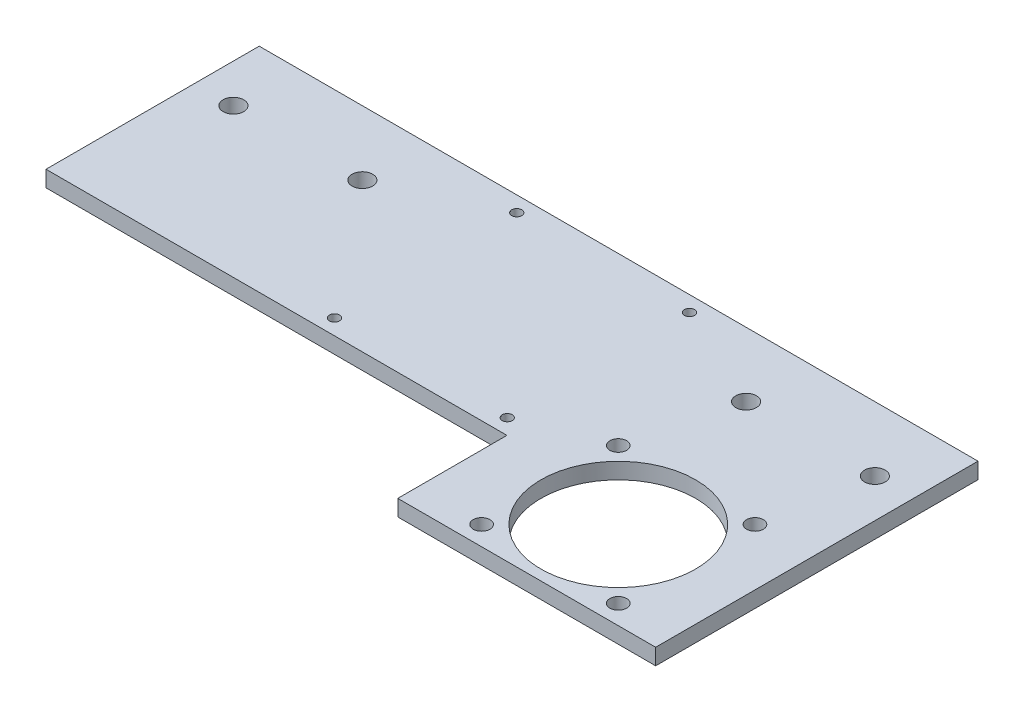
SolidWorks part; units mm, degrees
ref_plane "Front Plane" through (0, 0, 0) normal (0, 0, 1) x (1, 0, 0)
ref_plane "Top Plane" through (0, 0, 0) normal (0, 1, 0) x (1, 0, 0)
ref_plane "Right Plane" through (0, 0, 0) normal (1, 0, 0) x (0, 0, -1)
sketch "Sketch1" plane through (0, 0, 0) normal (0, 1, 0) x (1, 0, 0)
  line L1 (20, -21) -> (-20, -21)
  line L2 (20, -21) -> (20, 21)
  line L3 (20, 21) -> (-20, 21)
  line L4 (-20, -21) -> (-20, 21)
  line L5 (20, -21) -> (-20, 21) construction
  line L6 (20, 21) -> (-20, -21) construction
  point P0 (0, 0)
  dimension "D1" = 40
  dimension "D2" = 42
extrude "Boss-Extrude1" add sketch "Sketch1" along normal blind 3.175
sketch "Sketch2" plane through (0, 3.175, 0) normal (0, 1, 0) x (1, 0, 0)
  line L0 (20, -21) -> (20, 21) construction
  line L1 (-20, -21) -> (20, -21) construction
  line L2 (0, -21) -> (0, 21) construction
  line L3 (20, 21) -> (-20, 21) construction
  line L4 (20, 0) -> (-20, 0) construction
  line L5 (-20, 21) -> (-20, -21) construction
  line L6 (20, -21) -> (-20, -21) construction
  circle A0 centre (17.016, -17.952) radius 1
  circle A1 centre (-17.016, -17.952) radius 1
  circle A2 centre (17.016, 17.952) radius 1
  circle A3 centre (-17.016, 17.952) radius 1
  dimension "D1" = 2
  dimension "D2" = 17.016
  dimension "D3" = 3.048
extrude "Cut-Extrude1" cut sketch "Sketch2" against normal through all
sketch "Sketch3" plane through (0, 3.175, 0) normal (0, 1, 0) x (1, 0, 0)
  line L0 (20, 21) -> (-20, 21) construction
  line L1 (20, -42.5) -> (70.8, -42.5)
  line L2 (20, -42.5) -> (20, 21)
  line L3 (20, 21) -> (70.8, 21)
  line L4 (70.8, -42.5) -> (70.8, 21)
  line L5 (-20, 21) -> (-70.8, 21)
  line L6 (-20, 21) -> (-20, -42.5)
  line L7 (-20, -42.5) -> (-70.8, -42.5)
  line L8 (-70.8, 21) -> (-70.8, -42.5)
  line L10 (-20, -42.5) -> (-20, -67.9)
  dimension "D1" = 50.8
  dimension "D2" = 50.8
  dimension "D4" = 63.5
extrude "Boss-Extrude2" add sketch "Sketch3" against normal blind 3.175
sketch "Sketch4" plane through (0, 3.175, 0) normal (0, 1, 0) x (1, 0, 0)
  line L0 (70.8, 21) -> (-70.8, 21) construction
  line L1 (70.8, -42.5) -> (70.8, 21) construction
  line L2 (-70.8, 21) -> (-70.8, -42.5) construction
  circle A0 centre (63.18, 8.3) radius 2.032
  circle A1 centre (37.8145, 8.3) radius 2.032
  circle A2 centre (-37.78, 8.3) radius 2.032
  circle A3 centre (-63.18, 8.3) radius 2.032
  dimension "D1" = 4.064
  dimension "D6" = 4.064
  dimension "D7" = 4.064
  dimension "D8" = 4.064
  dimension "D2" = 12.7
  dimension "D3" = 7.62
  dimension "D4" = 25.3655
  dimension "D5" = 25.4
  dimension "D9" = 7.62
extrude "Cut-Extrude2" cut sketch "Sketch4" against normal through all
sketch "Sketch7" plane through (0, 0, 0) normal (0, -1, 0) x (1, 0, 0)
  line L0 (0, 21) -> (0, -21) construction
  line L1 (-20, 21) -> (20, 21) construction
  line L2 (70.8, -21) -> (-70.8, -21) construction
  line L3 (-70.8, 0) -> (70.8, 0) construction
  line L4 (-70.8, -21) -> (-70.8, 42.5) construction
  line L5 (70.8, 42.5) -> (70.8, -21) construction
sketch "Sketch8" plane through (0, 0, 0) normal (0, -1, 0) x (-1, 0, 0)
  line L0 (-20, -42.5) -> (-70.8, -42.5) construction
  line L1 (-20, -42.5) -> (-20, -21) construction
  line L2 (-70.8, -42.5) -> (-70.8, 21) construction
  circle A0 centre (-32.7, -38.69) radius 1.651
  circle A1 centre (-32.7, -11.766) radius 1.651
  circle A2 centre (-59.624, -38.69) radius 1.651
  circle A3 centre (-59.624, -11.766) radius 1.651
  dimension "D1" = 3.302
  dimension "D2" = 3.302
  dimension "D4" = 3.302
  dimension "D12" = 3.302
  dimension "D3" = 26.924
  dimension "D5" = 26.924
  dimension "D6" = 26.924
  dimension "D7" = 26.924
  dimension "D8" = 3.81
  dimension "D9" = 12.7
  dimension "D10" = 12.7
  dimension "D11" = 11.176
extrude "Cut-Extrude5" cut sketch "Sketch8" against normal through all
sketch "Sketch9" plane through (0, 0, 0) normal (0, -1, 0) x (-1, 0, 0)
  line L0 (-32.7, -38.69) -> (-32.7, -11.766) construction
  line L1 (-32.7, -11.766) -> (-59.624, -11.766) construction
  line L2 (-59.624, -11.766) -> (-59.624, -38.69) construction
  line L3 (-59.624, -38.69) -> (-32.7, -38.69) construction
  line L4 (-46.162, -38.69) -> (-46.162, -11.766) construction
  line L5 (-32.7, -25.228) -> (-59.624, -25.228) construction
  line L6 (0, -21) -> (0, 21) construction
  line L7 (20, -21) -> (-20, -21) construction
  line L8 (-70.8, 21) -> (70.8, 21) construction
  circle A0 centre (-46.162, -25.228) radius 15.24
  dimension "D1" = 30.48
extrude "Cut-Extrude6" cut sketch "Sketch9" against normal through all
sketch "Sketch10" plane through (0, 3.175, 0) normal (0, 1, 0) x (1, 0, 0)
  line L1 (-20, -21) -> (-70.8, -21)
  line L2 (-20, -21) -> (-20, -42.5)
  line L3 (-20, -42.5) -> (-70.8, -42.5)
  line L4 (-70.8, -21) -> (-70.8, -42.5)
extrude "Cut-Extrude7" cut sketch "Sketch10" against normal through all both and the other way through all
